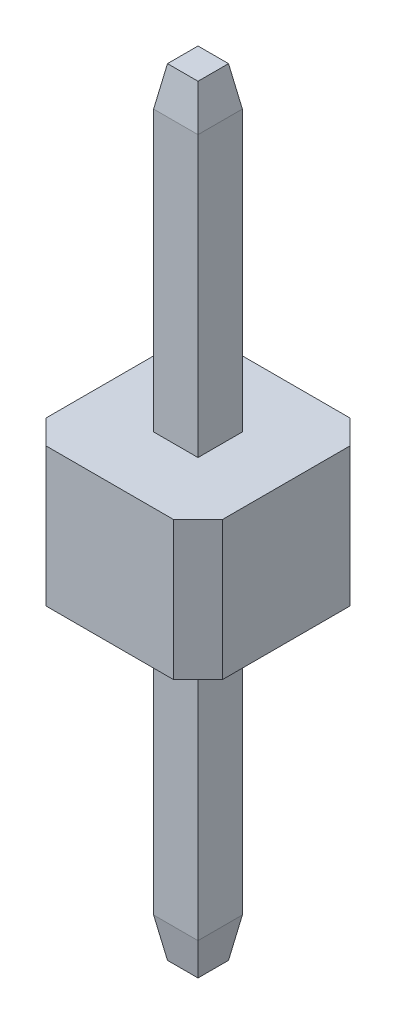
SolidWorks part; units mm, degrees
ref_plane "Alzado" through (0, 0, 0) normal (0, 0, 1) x (1, 0, 0)
ref_plane "Planta" through (0, 0, 0) normal (0, 1, 0) x (1, 0, 0)
ref_plane "Vista lateral" through (0, 0, 0) normal (1, 0, 0) x (0, 0, -1)
sketch "Croquis1" plane through (0, 0, 0) normal (0, 1, 0) x (1, 0, 0)
  line L0 (-1.27, 0.92) -> (-0.92, 1.27)
  line L1 (-0.92, 1.27) -> (0.92, 1.27)
  line L2 (-1.27, 0.92) -> (-1.27, -0.92)
  line L3 (-0.92, -1.27) -> (0.92, -1.27)
  line L4 (1.27, 0.92) -> (1.27, -0.92)
  line L5 (-1.27, 1.27) -> (1.27, -1.27) construction
  line L6 (-1.27, -1.27) -> (1.27, 1.27) construction
  line L7 (0.92, 1.27) -> (1.27, 0.92)
  line L8 (0.92, -1.27) -> (1.27, -0.92)
  line L9 (-1.27, -0.92) -> (-0.92, -1.27)
  point P0 (0, 0)
  dimension "D1" = 2.54
  dimension "D2" = 2.54
extrude "Saliente-Extruir1" add sketch "Croquis1" along normal mid plane 2
sketch "Croquis2" plane through (0, 0, 0) normal (0, 1, 0) x (1, 0, 0)
  line L1 (-0.32, 0.32) -> (0.32, 0.32)
  line L2 (-0.32, 0.32) -> (-0.32, -0.32)
  line L3 (-0.32, -0.32) -> (0.32, -0.32)
  line L4 (0.32, 0.32) -> (0.32, -0.32)
  line L5 (-0.32, 0.32) -> (0.32, -0.32) construction
  line L6 (-0.32, -0.32) -> (0.32, 0.32) construction
  point P0 (0, 0)
  dimension "D1" = 0.64
extrude "Saliente-Extruir2" add sketch "Croquis2" along normal mid plane 11.2
chamfer "Chaflán1" distance 0.1 angle 80 8 edges at (0, -5.6, -0.32) (0.32, -5.6, 0) (0, -5.6, 0.32) (-0.32, -5.6, 0) (0.32, 5.6, 0) (0, 5.6, -0.32) (-0.32, 5.6, 0) (0, 5.6, 0.32)
